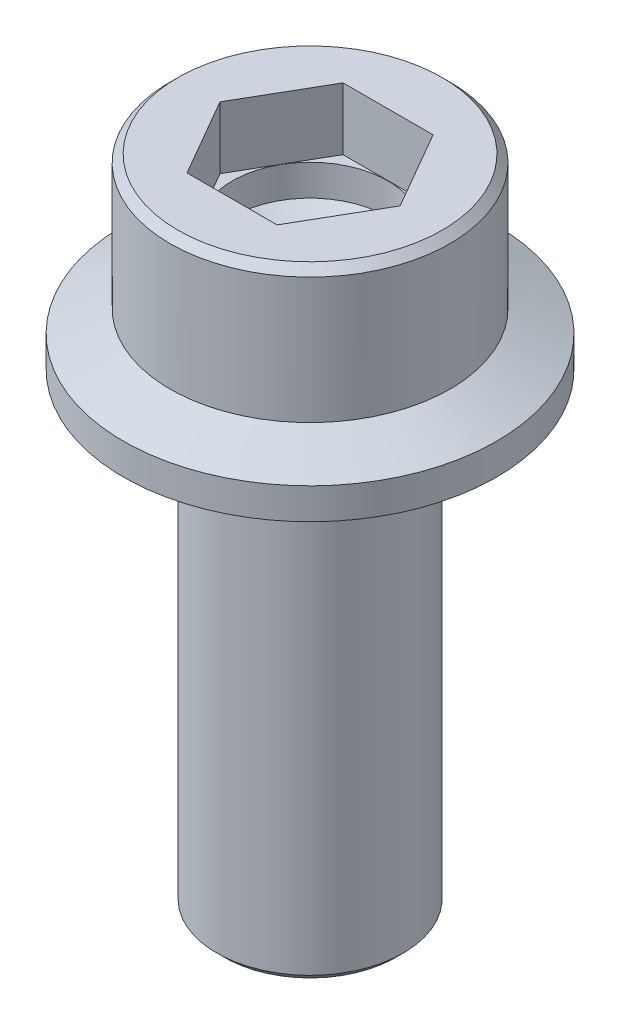
SolidWorks part; units mm, degrees
material "Steel (Zinc Flake)"
ref_plane "Front Plane" through (0, 0, 0) normal (0, 0, 1) x (1, 0, 0)
ref_plane "Top Plane" through (0, 0, 0) normal (0, 1, 0) x (1, 0, 0)
ref_plane "Right Plane" through (0, 0, 0) normal (1, 0, 0) x (0, 0, -1)
sketch "Sketch1" plane through (0, 0, 0) normal (0, 0, 1) x (1, 0, 0)
  line L0 (5, 42) -> (9, 42)
  line L1 (0, 0) -> (6, 0)
  line L2 (0, 0) -> (0, 32.9957)
  line L3 (6.4, 30) -> (12, 30)
  line L4 (6, 0) -> (6, 29.6)
  line L5 (9, 42) -> (9, 33.3989)
  line L6 (-12, 32) -> (-9, 33.3989) construction
  line L7 (12, 32) -> (12, 30)
  line L8 (-12, 32) -> (-12, 30) construction
  line L9 (5, 42) -> (5, 36)
  line L10 (-9, 42) -> (-9, 33.3989) construction
  line L11 (-6, 0) -> (-6, 30) construction
  line L12 (-6, 30) -> (-12, 30) construction
  line L13 (-9, 42) -> (-5, 42) construction
  line L14 (-6, 0) -> (0, 0) construction
  line L15 (12, 32) -> (9, 33.3989)
  line L16 (5, 36) -> (0, 32.9957)
  line L17 (-5.125, 30) -> (-5.125, 0) construction
  line L18 (5.125, 30) -> (5.125, 0) construction
  line L19 (-5, 42) -> (-5, 36) construction
  line L20 (-5, 36) -> (0, 32.9957) construction
  arc A0 (6.4, 30) -> (6, 29.6) centre (6.4, 29.6) ccw
  point P21 (6, 30)
  dimension "Radius-Under Head" = 0.4
  dimension "Major Dia." = 12
  dimension "D2" = 10
  dimension "Length" = 30
  dimension "D3" = 6
  dimension "Flange Width" = 24
  dimension "D4" = 118
  dimension "Head Height" = 12
  dimension "Head Dia." = 18
  dimension "Flange Thickness" = 2
  dimension "D7" = 25
  dimension "Minor Dia." = 10.25
  dimension "D12" = 3.3989
revolve "Main Body" add sketch "Sketch1" angle 360 about L2
cosmetic thread "Cosmetic Thread1" parameters "Thread Minor Dia."=6.9
sketch "Sketch2" plane through (0, 42, 0) normal (0, 1, 0) x (1, 0, 0)
  line L1 (-5.7908, 0) -> (-2.8954, -5.015)
  line L2 (-2.8954, -5.015) -> (2.8954, -5.015)
  line L3 (2.8954, -5.015) -> (5.7908, 0)
  line L4 (5.7908, 0) -> (2.8954, 5.015)
  line L5 (2.8954, 5.015) -> (-2.8954, 5.015)
  line L6 (-2.8954, 5.015) -> (-5.7908, 0)
  circle A0 centre (0, 0) radius 5.015 construction
  dimension "Hex Key" = 10.03
extrude "Hex Key 1" cut sketch "Sketch2" against normal blind 4
ref_plane "Plane1" through (0, 37.5, 0) normal (0, 1, 0) x (-1, 0, 0)
sketch "Sketch3" plane through (0, 37.5, 0) normal (0, 1, 0) x (-1, 0, 0)
  circle A0 centre (0, 0) radius 0.25
  dimension "D1" = 0.5
chamfer "Chamfer-Head" distance 0.5 1 edges at (0, 42, -9)
chamfer "Chamfer-Thread" distance 0.5 angle 45 1 edges at (0, 0, -6)
sketch "Sketch4" [suppressed] plane through (0, 0, 0) normal (0, 0, 1) x (1, 0, 0)
  line L0 (5, 21.6) -> (4.6, 22) construction
  line L1 (5, 18.1829) -> (5, 21.6) construction
  line L2 (4.6, 22) -> (-4.6, 22) construction
  line L3 (5, 21.6) -> (4.6, 22)
  line L4 (5, 21.6) -> (5, 22)
  line L5 (4.6, 22) -> (5, 22)
  line L6 (0, 0) -> (0, 22.5792) construction
revolve "Simplified" [suppressed] add sketch "Sketch4" angle 360 about L6
equation "\"Weight kg\"= round ( \"SW-Mass\" , 2 )"
equation "\"Weight lbs\"= round ( \"SW-Mass\" * 2.2046 , 2 )"
